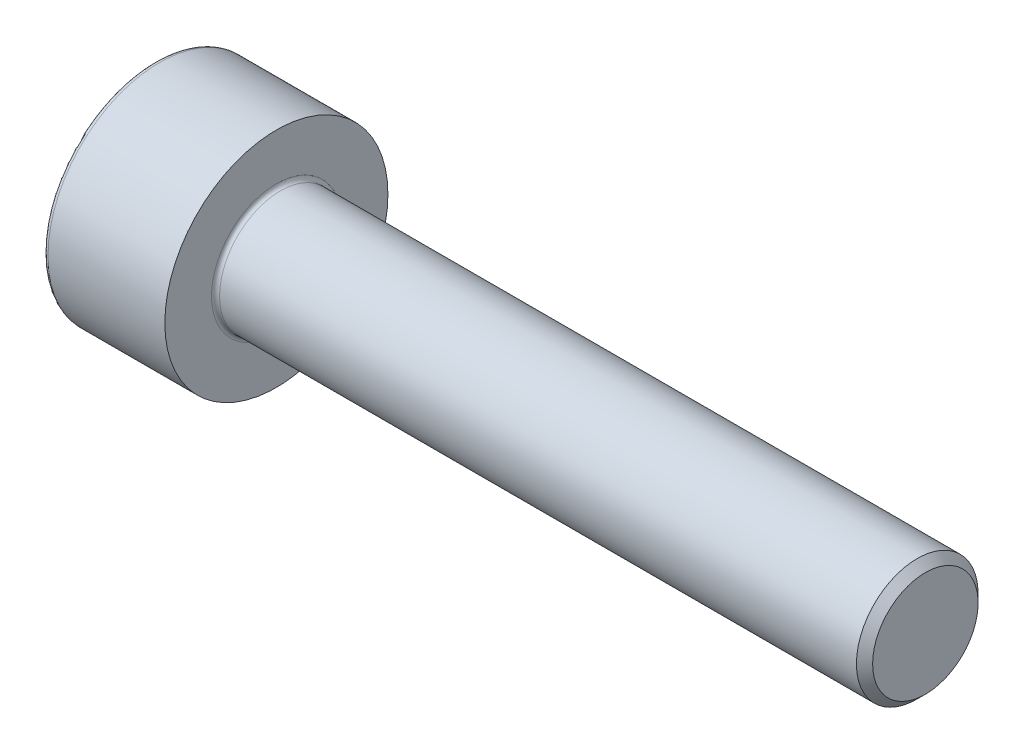
SolidWorks part; units mm, degrees
material "AISI Тип A2 Инструментальная сталь"
ref_plane "Front Plane" through (0, 0, 0) normal (0, 0, 1) x (1, 0, 0)
ref_plane "Top Plane" through (0, 0, 0) normal (0, 1, 0) x (1, 0, 0)
ref_plane "Right Plane" through (0, 0, 0) normal (1, 0, 0) x (0, 0, -1)
sketch "Sketch1" plane through (0, 0, 0) normal (0, 0, 1) x (1, 0, 0)
  line L0 (0, 0) -> (0, 2.75)
  line L1 (0, 2.75) -> (3, 2.75)
  line L2 (3, 2.75) -> (3, 0)
  line L3 (0, 0) -> (4.2799, 0) construction
  line L4 (3, 0) -> (19, 0)
  line L5 (19, 0) -> (19, 1.5)
  line L6 (19, 1.5) -> (3, 1.5)
  dimension "D1" = 16
  dimension "D2" = 3
  dimension "D3" = 2.75
  dimension "D4" = 1.5
revolve "Revolve1" add sketch "Sketch1" angle 360 about L3
fillet "Fillet1" radius 0.1 1 edges at (3, 0, 1.5)
fillet "Fillet2" radius 0.12 1 edges at (0, 0, 2.75)
chamfer "Chamfer1" distance 0.2 angle 45 1 edges at (19, 0, 1.5)
sketch "Sketch2" plane through (0, 0, 0) normal (-1, 0, 0) x (0, 0, 1)
  line L1 (0, 1.4434) -> (-1.25, 0.7217)
  line L2 (-1.25, 0.7217) -> (-1.25, -0.7217)
  line L3 (-1.25, -0.7217) -> (0, -1.4434)
  line L4 (0, -1.4434) -> (1.25, -0.7217)
  line L5 (1.25, -0.7217) -> (1.25, 0.7217)
  line L6 (1.25, 0.7217) -> (0, 1.4434)
  circle A0 centre (0, 0) radius 1.25 construction
extrude "Extrude1" cut sketch "Sketch2" against normal blind 1.3
